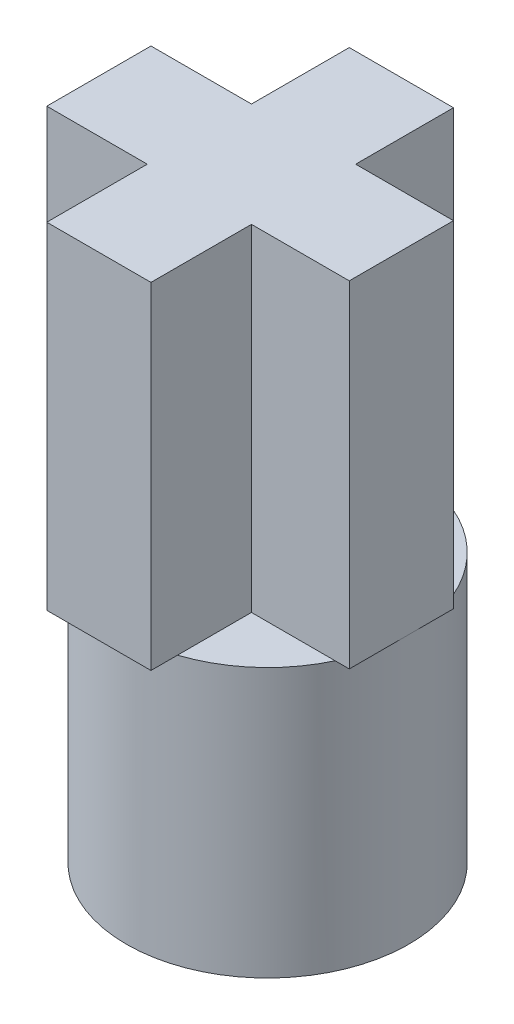
SolidWorks part; units mm, degrees
ref_plane "Front Plane" through (0, 0, 0) normal (0, 0, 1) x (1, 0, 0)
ref_plane "Top Plane" through (0, 0, 0) normal (0, 1, 0) x (1, 0, 0)
ref_plane "Right Plane" through (0, 0, 0) normal (1, 0, 0) x (0, 0, -1)
sketch "Sketch1" plane through (0, 0, 0) normal (0, 1, 0) x (1, 0, 0)
  circle A0 centre (0, 0) radius 2.1
  dimension "D1" = 4.2
extrude "Boss-Extrude1" add sketch "Sketch1" along normal blind 4 contours A0
sketch "Sketch2" plane through (0, 0, 0) normal (0, -1, 0) x (-1, 0, 0)
  circle A0 centre (0, 0) radius 1.6
  dimension "D1" = 3.2
extrude "Cut-Extrude1" cut sketch "Sketch2" against normal blind 3
sketch "Sketch3" plane through (0, 4, 0) normal (0, 1, 0) x (1, 0, 0)
  line L0 (-0.895, 0.655) -> (-2.39, 0.655)
  line L1 (0.655, -2.39) -> (-0.895, -2.39)
  line L2 (0.655, -2.39) -> (0.655, -0.895)
  line L3 (0.655, 2.11) -> (-0.895, 2.11)
  line L4 (-0.895, -2.39) -> (-0.895, -0.895)
  line L7 (2.11, -0.895) -> (0.655, -0.895)
  line L8 (2.11, -0.895) -> (2.11, 0.655)
  line L9 (2.11, 0.655) -> (0.655, 0.655)
  line L10 (-2.39, -0.895) -> (-2.39, 0.655)
  line L17 (0.655, 0.655) -> (0.655, 2.11)
  line L18 (-0.895, -0.895) -> (-2.39, -0.895)
  line L19 (-0.895, 0.655) -> (-0.895, 2.11)
  circle A1 centre (0, 0) radius 2.1 construction
  point P6 (0, 0)
  dimension "D1" = 1.55
  dimension "D2" = 4.5
  dimension "D3" = 0.895
  dimension "D4" = 2.39
  dimension "D5" = 4.5
  dimension "D6" = 1.55
  dimension "D7" = 2.39
  dimension "D8" = 0.895
extrude "Boss-Extrude2" add sketch "Sketch3" along normal blind 5
